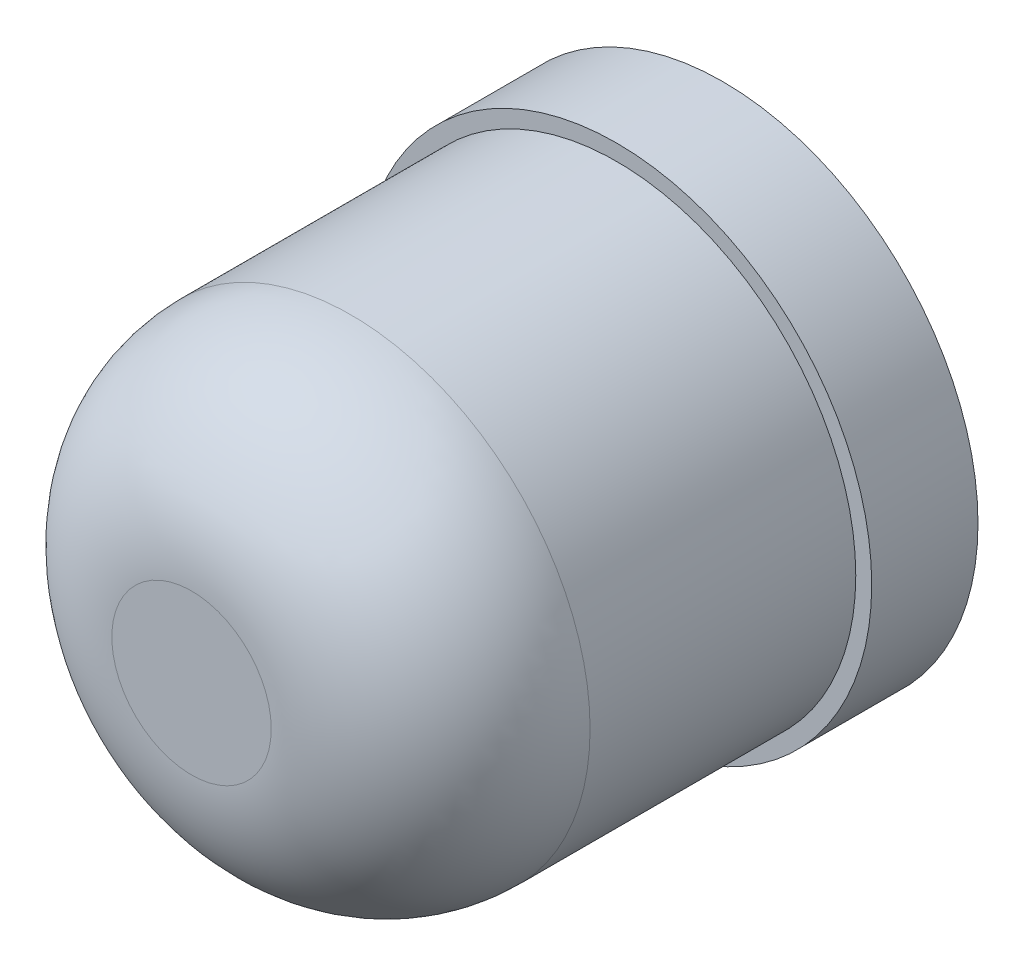
SolidWorks part; units mm, degrees
material "SMA"
ref_plane "Спереди" through (0, 0, 0) normal (0, 0, 1) x (1, 0, 0)
ref_plane "Сверху" through (0, 0, 0) normal (0, 1, 0) x (1, 0, 0)
ref_plane "Справа" through (0, 0, 0) normal (1, 0, 0) x (0, 0, -1)
sketch "Эскиз1" plane through (0, 0, 0) normal (0, 0, 1) x (1, 0, 0)
  circle A0 centre (0, 4.957) radius 2.25
extrude "Бобышка-Вытянуть1" add sketch "Эскиз1" along normal blind 4
sketch "Эскиз2" plane through (0, 0, 0) normal (0, 0, -1) x (-1, 0, 0)
  line L0 (0, 5.6062) -> (0, 4.2902) construction
  line L1 (-0.1616, 4.957) -> (0.1914, 4.957) construction
  circle A0 centre (0, 4.957) radius 2.4
extrude "Бобышка-Вытянуть2" add sketch "Эскиз2" along normal blind 1
fillet "Скругление8" radius 1.5 1 edges at (2.25, 4.957, 4)
